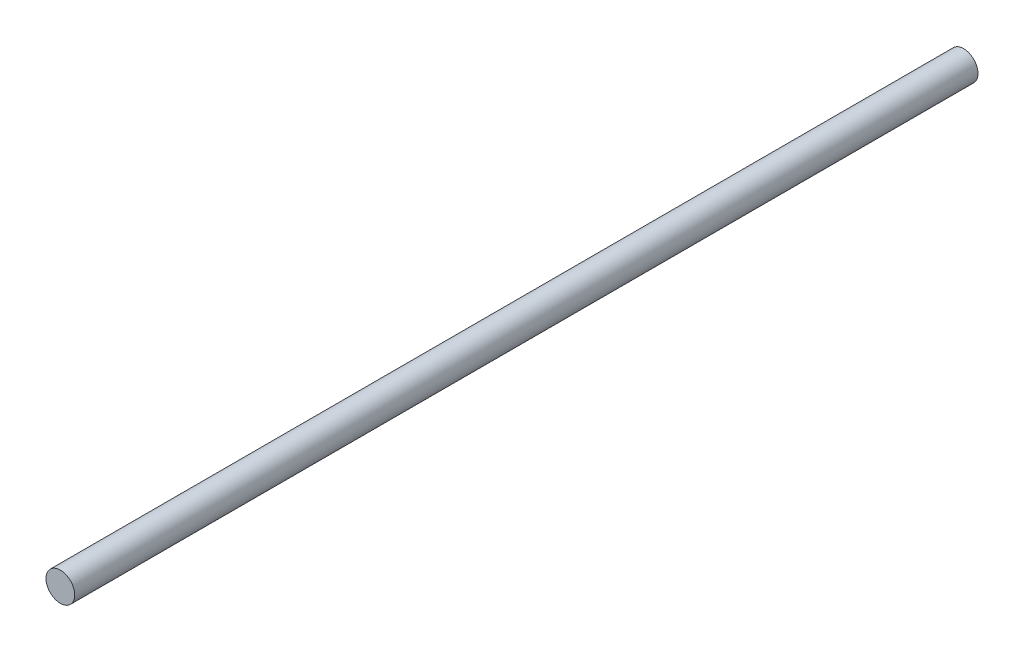
SolidWorks part; units mm, degrees
ref_plane "Front Plane" through (0, 0, 0) normal (0, 0, 1) x (1, 0, 0)
ref_plane "Top Plane" through (0, 0, 0) normal (0, 1, 0) x (1, 0, 0)
ref_plane "Right Plane" through (0, 0, 0) normal (1, 0, 0) x (0, 0, -1)
sketch "Sketch1" plane through (0, 0, 0) normal (0, 0, 1) x (1, 0, 0)
  circle A0 centre (0, 0) radius 8
  dimension "D1" = 16
extrude "Boss-Extrude1" add sketch "Sketch1" along normal mid plane 502
